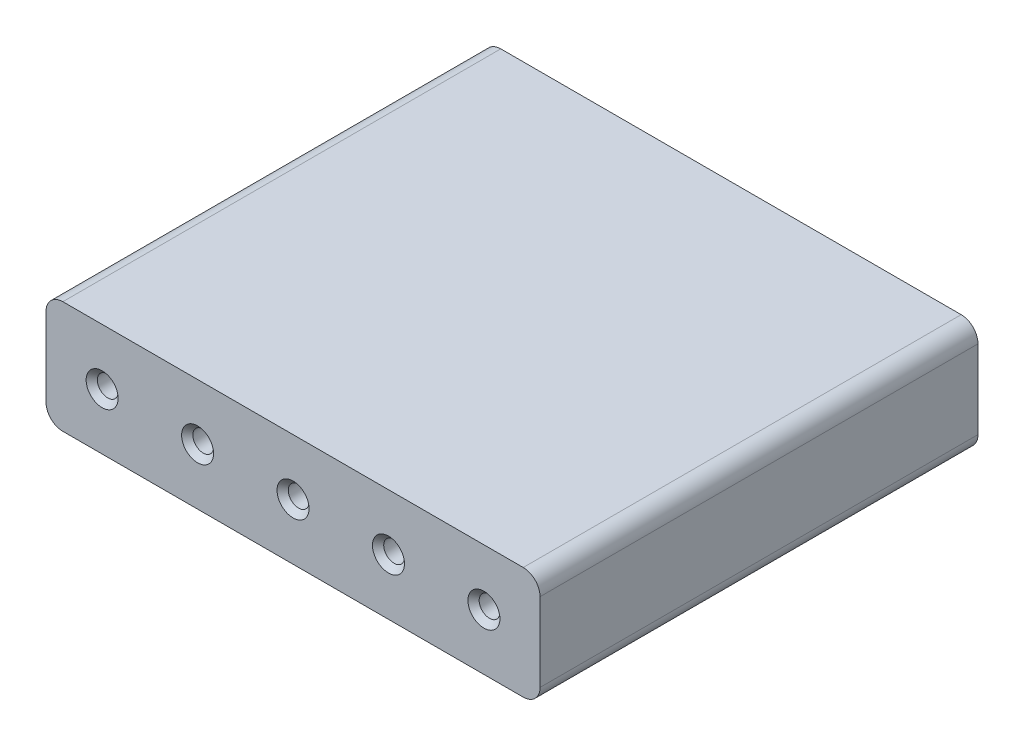
SolidWorks part; units mm, degrees
ref_plane "Front Plane" through (0, 0, 0) normal (0, 0, 1) x (1, 0, 0)
ref_plane "Top Plane" through (0, 0, 0) normal (0, 1, 0) x (1, 0, 0)
ref_plane "Right Plane" through (0, 0, 0) normal (1, 0, 0) x (0, 0, -1)
sketch "Sketch1" plane through (0, 0, 0) normal (0, 0, 1) x (1, 0, 0)
  line L1 (41, -10) -> (-41, -10)
  line L2 (44, -7) -> (44, 7)
  line L3 (41, 10) -> (-41, 10)
  line L4 (-44, -7) -> (-44, 7)
  line L5 (44, -10) -> (-44, 10) construction
  line L6 (44, 10) -> (-44, -10) construction
  circle A0 centre (-34, 0) radius 1.85
  circle A1 centre (-17, 0) radius 1.85
  circle A2 centre (0, 0) radius 1.85
  circle A3 centre (17, 0) radius 1.85
  circle A4 centre (34, 0) radius 1.85
  arc A5 (44, 7) -> (41, 10) centre (41, 7) ccw
  arc A6 (41, -10) -> (44, -7) centre (41, -7) ccw
  arc A7 (-41, -10) -> (-44, -7) centre (-41, -7) cw
  arc A8 (-41, 10) -> (-44, 7) centre (-41, 7) ccw
  point P0 (0, 0)
  point P9 (0, 0)
  point P17 (0, 0)
  point P18 (34, 0)
  dimension "D3" = 3.7
  dimension "D4" = 3
  dimension "D2" = 17
  dimension "D5" = 20
  dimension "D6" = 10
  dimension "D1" = 5
extrude "Boss-Extrude1" add sketch "Sketch1" along normal blind 78
chamfer "Chamfer1" distance 1 angle 45 10 edges at (18.85, 0, 0) (1.85, 0, 0) (-15.15, 0, 0) (-32.15, 0, 0) (35.85, 0, 0) (35.85, 0, 78) (1.85, 0, 78) (-15.15, 0, 78) (18.85, 0, 78) (-32.15, 0, 78)
